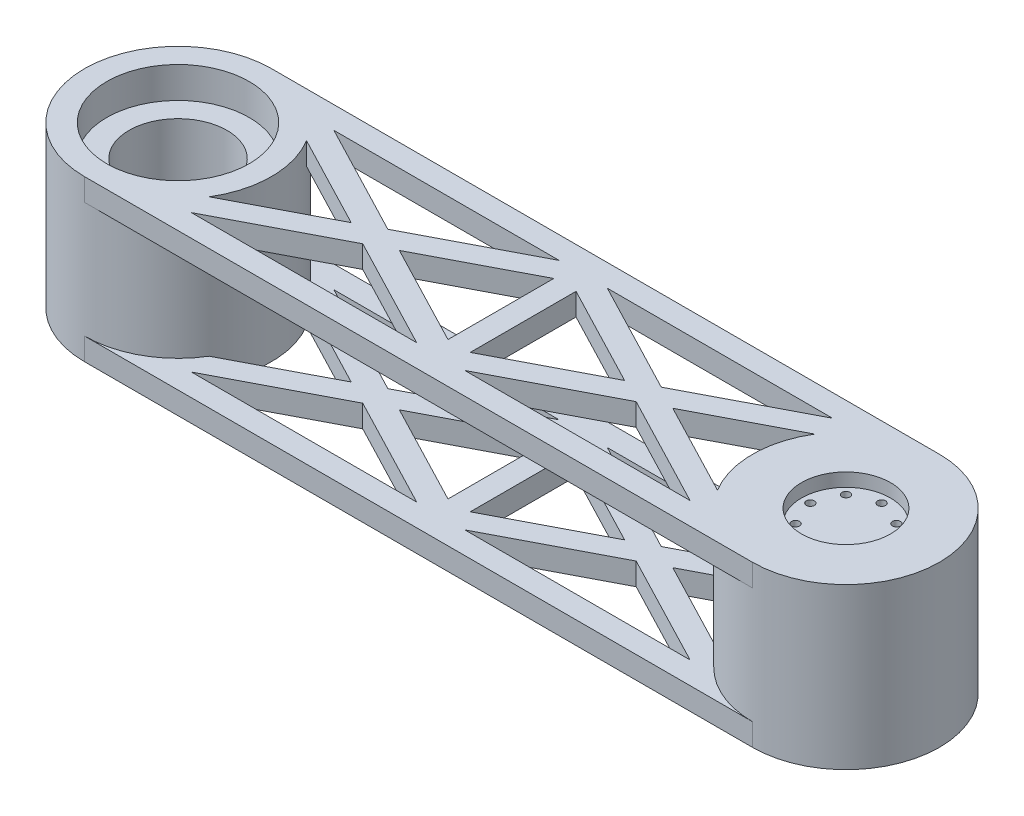
SolidWorks part; units mm, degrees
ref_plane "정면" through (0, 0, 0) normal (0, 0, 1) x (1, 0, 0)
ref_plane "윗면" through (0, 0, 0) normal (0, 1, 0) x (1, 0, 0)
ref_plane "우측면" through (0, 0, 0) normal (1, 0, 0) x (0, 0, -1)
sketch "스케치1" plane through (0, 0, 0) normal (0, 1, 0) x (1, 0, 0)
  circle A0 centre (68.9106, -5.2941) radius 21
  circle A1 centre (-81.0894, -5.2941) radius 21
  circle A2 centre (-81.0894, -5.2941) radius 16
  circle A3 centre (68.9106, -5.2941) radius 10
  dimension "D1" = 42
  dimension "D2" = 42
  dimension "D5" = 32
  dimension "D6" = 20
  dimension "D3" = 150
  dimension "D4" = 0
extrude "보스-돌출1" add sketch "스케치1" along normal blind 36
sketch "스케치2" plane through (0, 36, 0) normal (0, 1, 0) x (1, 0, 0)
  line L0 (-81.0894, -26.2941) -> (68.9106, -26.2941)
  line L1 (-81.0894, 15.7059) -> (68.9106, 15.7059)
  line L2 (-81.0894, -21.2941) -> (68.9106, -21.2941)
  line L3 (-81.0894, 10.7059) -> (68.9106, 10.7059)
  line L4 (-81.0894, -26.2941) -> (-81.0894, -21.2941)
  line L5 (68.9106, -26.2941) -> (68.9106, -21.2941)
  line L6 (68.9106, 10.7059) -> (68.9106, 15.7059)
  line L7 (-81.0894, 10.7059) -> (-81.0894, 15.7059)
  circle A1 centre (-81.0894, -5.2941) radius 21 construction
  circle A3 centre (68.9106, -5.2941) radius 21 construction
  circle A4 centre (-81.0894, -5.2941) radius 16 construction
  dimension "D1" = 21
  dimension "D2" = 21
  dimension "D3" = 5
  dimension "D4" = 5
extrude "보스-돌출3" add sketch "스케치2" against normal blind 5
sketch "스케치3" plane through (0, 0, 0) normal (0, -1, 0) x (1, 0, 0)
  line L0 (68.9106, -15.7059) -> (-81.0894, -15.7059)
  line L1 (68.9106, 26.2941) -> (-81.0894, 26.2941)
  line L2 (68.9106, 26.2941) -> (68.9106, 21.2941)
  line L3 (68.9106, -10.7059) -> (68.9106, -15.7059)
  line L4 (68.9106, 21.2941) -> (-81.0894, 21.2941)
  line L6 (-81.0894, -10.7059) -> (68.9106, -10.7059)
  line L7 (-81.0894, 26.2941) -> (-81.0894, 21.2941)
  line L8 (-81.0894, -10.7059) -> (-81.0894, -15.7059)
  circle A0 centre (68.9106, 5.2941) radius 21 construction
  circle A1 centre (-81.0894, 5.2941) radius 21 construction
  circle A3 centre (-81.0894, 5.2941) radius 16 construction
extrude "보스-돌출4" add sketch "스케치3" against normal blind 5
sketch "스케치4" plane through (0, 0, 0) normal (0, -1, 0) x (1, 0, 0)
  line L0 (-6.0894, 21.2941) -> (-6.0894, -10.7059) construction
  line L1 (-67.488, 21.2941) -> (55.3091, 21.2941) construction
  line L2 (55.3091, -10.7059) -> (-67.488, -10.7059) construction
  line L3 (-6.0894, -10.7059) -> (55.3091, 21.2941) construction
  line L4 (-36.7887, 8.1132) -> (-7.2449, 23.511)
  line L5 (55.3091, -10.7059) -> (-6.0894, 21.2941) construction
  line L6 (-67.488, -10.7059) -> (-6.0894, 21.2941) construction
  line L7 (-67.488, 21.2941) -> (-6.0894, -10.7059) construction
  line L8 (-6.0894, 21.2941) -> (-7.2449, 23.511)
  line L9 (-4.934, -12.9229) -> (24.6098, 2.4749)
  line L10 (56.4646, -8.489) -> (30.019, 5.2941)
  line L11 (-66.3325, -12.9229) -> (-36.7887, 2.4749)
  line L12 (-68.6434, 19.0771) -> (-42.1978, 5.2941)
  line L13 (-31.3795, 5.2941) -> (-8.5894, -6.5838)
  line L14 (54.1537, -12.9229) -> (24.6098, 2.4749)
  line L15 (-68.6434, -8.489) -> (-42.1978, 5.2941)
  line L16 (-66.3325, 23.511) -> (-36.7887, 8.1132)
  line L17 (-68.6434, 19.0771) -> (-66.3325, 23.511)
  line L18 (-68.6434, -8.489) -> (-66.3325, -12.9229)
  line L19 (-36.7887, 2.4749) -> (-7.2449, -12.9229)
  line L20 (-6.0894, 21.2941) -> (-4.934, 23.511)
  line L21 (-68.6434, -8.489) -> (-7.2449, 23.511) construction
  line L22 (54.1537, -12.9229) -> (56.4646, -8.489)
  line L23 (-7.2449, -12.9229) -> (-4.934, -12.9229)
  line L24 (54.1537, 23.511) -> (56.4646, 19.0771)
  line L26 (-3.5894, -6.5838) -> (19.2007, 5.2941)
  line L27 (-66.3325, 23.511) -> (-4.934, -8.489) construction
  line L32 (24.6098, 8.1132) -> (54.1537, 23.511)
  line L33 (-31.3795, 5.2941) -> (-8.5894, 17.1719)
  line L34 (19.2007, 5.2941) -> (-3.5894, 17.1719)
  line L35 (30.019, 5.2941) -> (56.4646, 19.0771)
  line L36 (54.1537, -12.9229) -> (-7.2449, 19.0771) construction
  line L37 (24.6098, 8.1132) -> (-4.934, 23.511)
  line L38 (-4.934, -12.9229) -> (56.4646, 19.0771) construction
  line L39 (-8.5894, 17.1719) -> (-8.5894, -6.5838)
  line L40 (56.4646, -8.489) -> (-4.934, 23.511) construction
  line L41 (-68.6434, 19.0771) -> (-7.2449, -12.9229) construction
  line L42 (-66.3325, -12.9229) -> (-4.934, 19.0771) construction
  line L43 (-3.5894, 17.1719) -> (-3.5894, -6.5838)
  arc A0 (-67.488, -10.7059) -> (-67.488, 21.2941) centre (-81.0894, 5.2941) ccw construction
  point P15 (-6.0894, 5.2941)
  point P17 (-8.5894, 21.2941)
  point P18 (-8.5894, -10.7059)
  point P19 (-3.5894, 21.2941)
  point P20 (-3.5894, -10.7059)
  point P29 (-7.2449, -8.489)
  dimension "D3" = 2.5
  dimension "D4" = 2.5
extrude "보스-돌출5" add sketch "스케치4" against normal blind 5
sketch "스케치7" plane through (0, 36, 0) normal (0, 1, 0) x (1, 0, 0)
  circle A0 centre (68.9106, -5.2941) radius 16
extrude "보스-돌출7" add sketch "스케치7" against normal blind 30 from offset 3 offset against normal yes
sketch "스케치8" plane through (0, 33, 0) normal (0, 1, 0) x (1, 0, 0)
  line L0 (68.9106, 2.7059) -> (68.9106, -13.2941) construction
  line L1 (68.9106, -5.2941) -> (74.5674, 0.3628) construction
  line L2 (60.9106, -5.2941) -> (76.9106, -5.2941) construction
  line L3 (68.9106, -5.2941) -> (63.2537, 0.3628) construction
  line L4 (63.2537, 0.3628) -> (74.5674, -10.9509) construction
  line L5 (68.9106, -5.2941) -> (63.2537, -10.9509) construction
  circle A0 centre (68.9106, -5.2941) radius 8 construction
  circle A1 centre (76.9106, -5.2941) radius 0.9
  circle A2 centre (68.9106, 2.7059) radius 0.9
  circle A3 centre (74.5674, 0.3628) radius 0.9
  circle A4 centre (63.2537, 0.3628) radius 0.9
  circle A5 centre (60.9106, -5.2941) radius 0.9
  circle A6 centre (68.9106, -13.2941) radius 0.9
  circle A7 centre (63.2537, -10.9509) radius 0.9
  circle A8 centre (74.5674, -10.9509) radius 0.9
  dimension "D4" = 1.8
  dimension "D5" = 1.8
  dimension "D6" = 1.8
extrude "컷-돌출1" cut sketch "스케치8" against normal blind 8
ref_plane "평면1" through (0, 18, 0) normal (0, 1, 0) x (1, 0, 0)
mirror "대칭 복사1" about plane through (0, 18, 0) normal (0, 1, 0) of "컷-돌출1"
mirror "대칭 복사2" about plane through (0, 18, 0) normal (0, 1, 0) of "보스-돌출5"
sketch "스케치9" plane through (0, 36, 0) normal (0, 1, 0) x (1, 0, 0)
  circle A0 centre (-81.0894, -5.2941) radius 16
  dimension "D1" = 32
sketch "스케치10" plane through (0, 36, 0) normal (0, 1, 0) x (1, 0, 0)
  circle A0 centre (-81.0894, -5.2941) radius 18.2432
  circle A1 centre (-81.0894, -5.2941) radius 11
  dimension "D1" = 22
extrude "보스-돌출8" add sketch "스케치10" against normal blind 22 from offset 7
